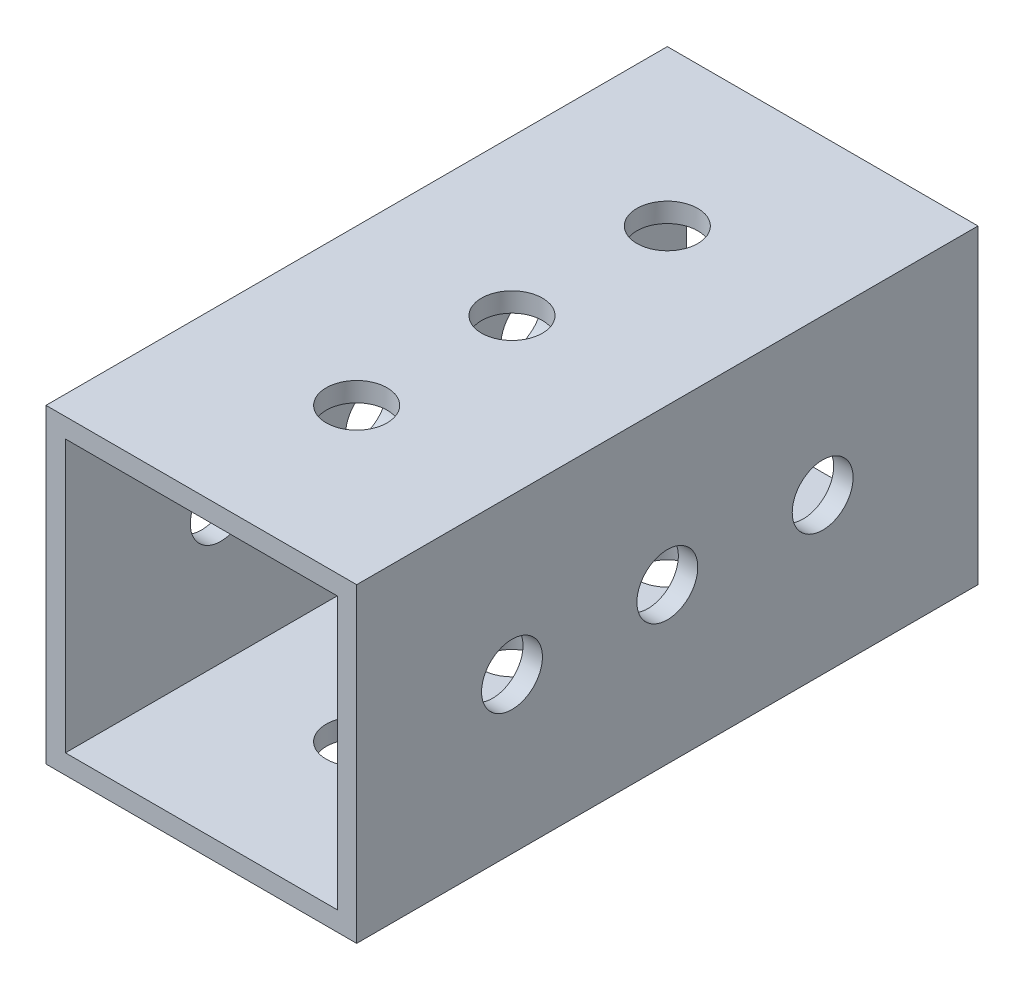
SolidWorks part; units mm, degrees
material "6061 Alloy"
ref_plane "Front Plane" through (0, 0, 0) normal (0, 0, 1) x (1, 0, 0)
ref_plane "Top Plane" through (0, 0, 0) normal (0, 1, 0) x (1, 0, 0)
ref_plane "Right Plane" through (0, 0, 0) normal (1, 0, 0) x (0, 0, -1)
sketch "Sketch1" plane through (0, 0, 0) normal (0, 0, 1) x (1, 0, 0)
  line L0 (1.5875, 1.5875) -> (23.8125, 1.5875)
  line L1 (0, 0) -> (25.4, 0)
  line L2 (0, 0) -> (0, 25.4)
  line L3 (0, 25.4) -> (25.4, 25.4)
  line L4 (25.4, 0) -> (25.4, 25.4)
  line L5 (23.8125, 1.5875) -> (23.8125, 23.8125)
  line L6 (1.5875, 23.8125) -> (23.8125, 23.8125)
  line L7 (1.5875, 1.5875) -> (1.5875, 23.8125)
  dimension "D1" = 25.4
  dimension "D2" = 1.5875
extrude "Boss-Extrude1" add sketch "Sketch1" along normal blind 50.8
sketch "Sketch2" plane through (0, 25.4, 0) normal (0, 1, 0) x (1, 0, 0)
  line L0 (25.4, 0) -> (0, 0) construction
  line L1 (12.7, -12.7) -> (12.7, -25.4) construction
  circle A0 centre (12.7, -12.7) radius 2.4892
  circle A1 centre (12.7, -25.4) radius 2.4892
  circle A2 centre (12.7, -38.1) radius 2.4892
  point P4 (12.7, 0)
  dimension "D1" = 4.9784
  dimension "D2" = 12.7
  dimension "D4" = 12.7
  dimension "D3" = 3
extrude "Cut-Extrude1" cut sketch "Sketch2" against normal through all
sketch "Sketch3" plane through (0, 0, 0) normal (-1, 0, 0) x (0, 0, 1)
  line L0 (0, 25.4) -> (0, 0) construction
  line L1 (12.7, 12.7) -> (25.4, 12.7) construction
  circle A0 centre (12.7, 12.7) radius 2.4892
  circle A1 centre (25.4, 12.7) radius 2.4892
  circle A2 centre (38.1, 12.7) radius 2.4892
  point P4 (0, 12.7)
  dimension "D1" = 4.9784
  dimension "D2" = 12.7
  dimension "D4" = 12.7
  dimension "D3" = 3
extrude "Cut-Extrude2" cut sketch "Sketch3" against normal through all
